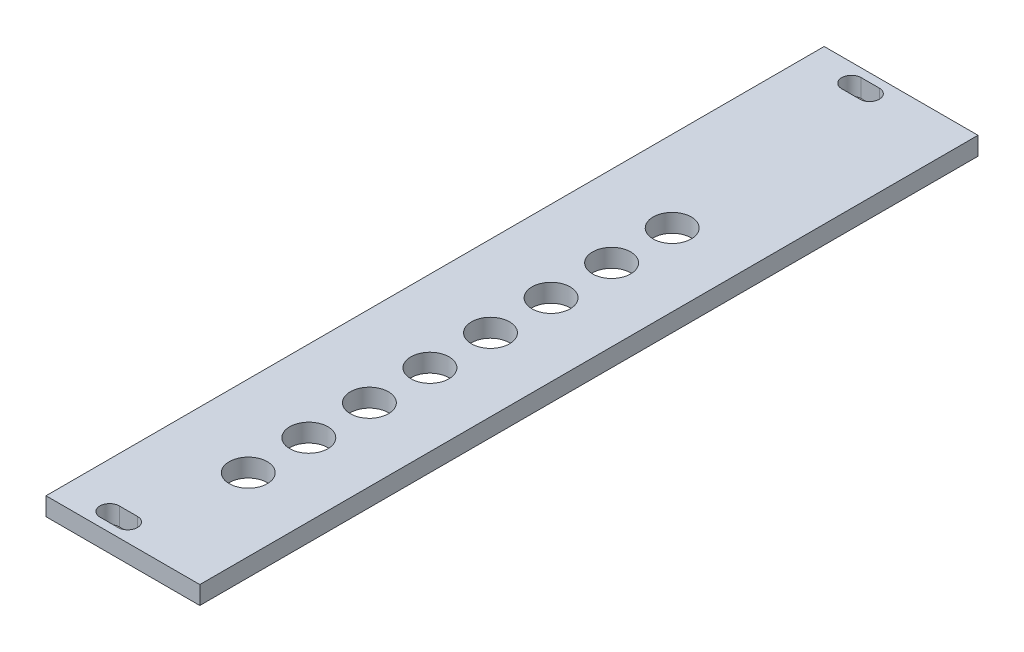
SolidWorks part; units mm, degrees
material "S235JR"
ref_plane "Vorderansicht (XY)" through (0, 0, 0) normal (0, 0, 1) x (1, 0, 0)
ref_plane "Draufansicht (XZ)" through (0, 0, 0) normal (0, 1, 0) x (1, 0, 0)
ref_plane "Seitenansicht (ZY)" through (0, 0, 0) normal (1, 0, 0) x (0, 0, -1)
sketch "Skizze1" plane through (0, 0, 0) normal (0, 1, 0) x (1, 0, 0)
  line L1 (-12.7, -64.25) -> (12.7, -64.25)
  line L2 (-12.7, -64.25) -> (-12.7, 64.25)
  line L3 (-12.7, 64.25) -> (12.7, 64.25)
  line L4 (12.7, -64.25) -> (12.7, 64.25)
  line L5 (-12.7, -64.25) -> (12.7, 64.25) construction
  line L6 (-12.7, 64.25) -> (12.7, -64.25) construction
  point P0 (0, 0)
  dimension "D1" = 128.5
  dimension "D2" = 25.4
extrude "Aufsatz-Linear austragen1" add sketch "Skizze1" along normal blind 3
sketch "Skizze2" plane through (0, 0, 0) normal (0, 1, 0) x (1, 0, 0)
  line L0 (-5.2, 61.25) -> (-2.2, 61.25) construction
  line L1 (-5.2, 62.85) -> (-2.2, 62.85)
  line L2 (-5.2, 59.65) -> (-2.2, 59.65)
  line L3 (-12.7, -64.25) -> (-12.7, 64.25) construction
  line L5 (-5.2, -61.25) -> (-2.2, -61.25) construction
  line L6 (-5.2, -59.65) -> (-2.2, -59.65)
  line L7 (-5.2, -62.85) -> (-2.2, -62.85)
  line L9 (12.7, 64.25) -> (-12.7, 64.25) construction
  line L10 (-12.7, -64.25) -> (12.7, -64.25) construction
  arc A0 (-5.2, 62.85) -> (-5.2, 59.65) centre (-5.2, 61.25) ccw
  arc A1 (-2.2, 59.65) -> (-2.2, 62.85) centre (-2.2, 61.25) ccw
  arc A2 (-5.2, -59.65) -> (-5.2, -62.85) centre (-5.2, -61.25) ccw
  arc A3 (-2.2, -62.85) -> (-2.2, -59.65) centre (-2.2, -61.25) ccw
  point P2 (-3.7, 61.25)
  point P13 (-3.7, -61.25)
  dimension "D1" = 7.5
  dimension "D2" = 3.2
  dimension "D3" = 3
  dimension "D4" = 3
  dimension "D5" = 7.5
  dimension "D6" = 3
  dimension "D7" = 3.2
  dimension "D8" = 3
extrude "Schnitt-Linear austragen4" cut sketch "Skizze2" along normal through all
sketch "Skizze3" plane through (0, 0, 0) normal (0, 1, 0) x (1, 0, 0)
  line L0 (-12.7, -64.25) -> (12.7, -64.25) construction
  line L1 (12.7, -64.25) -> (12.7, 64.25) construction
  circle A0 centre (0.7, -44.25) radius 3.15
  circle A1 centre (0.7, -34.25) radius 3.15
  circle A2 centre (0.7, -24.25) radius 3.15
  circle A3 centre (0.7, -14.25) radius 3.15
  circle A4 centre (0.7, -4.25) radius 3.15
  circle A5 centre (0.7, 5.75) radius 3.15
  circle A6 centre (0.7, 15.75) radius 3.15
  circle A7 centre (0.7, 25.75) radius 3.15
  dimension "D1" = 6.3
  dimension "D3" = 20
  dimension "D4" = 12
  dimension "D2" = 8
extrude "Schnitt-Linear austragen6" cut sketch "Skizze3" along normal through all
sketch "Skizze5" plane through (0, 0, 0) normal (0, 1, 0) x (1, 0, 0)
  line L0 (-7.6982, 50.7231) -> (-8.9305, 50.7231)
  line L1 (-10.1805, 51.9731) -> (-10.1805, 52.4731)
  line L2 (-8.9305, 53.7231) -> (-7.6982, 53.7231)
  line L3 (-6.8144, 54.0892) -> (-4.1805, 56.7231)
  line L4 (-4.1805, 56.7231) -> (-4.1805, 54.2408)
  line L5 (-4.5466, 53.357) -> (-6.8144, 51.0892)
  arc A0 (-4.1805, 54.2408) -> (-4.5466, 53.357) centre (-5.4305, 54.2408) cw
  arc A1 (-7.6982, 50.7231) -> (-6.8144, 51.0892) centre (-7.6982, 51.9731) ccw
  arc A2 (-7.6982, 53.7231) -> (-6.8144, 54.0892) centre (-7.6982, 54.9731) ccw
  arc A3 (-10.1805, 52.4731) -> (-8.9305, 53.7231) centre (-8.9305, 52.4731) cw
  arc A4 (-8.9305, 50.7231) -> (-10.1805, 51.9731) centre (-8.9305, 51.9731) cw
  text T0 "CTAG" font "Earthbound" height 3.5
  text T1 "Splitter\r\n" font "Earthbound" height 3.5
  text T2 "="
  text T3 "="
  text T4 "+"
  text T5 "="
  text T6 "+"
  text T7 "="
  text T8 "="
  text T9 "="
  point P18 (-4.1805, 53.7231)
  point P21 (-7.1805, 50.7231)
  point P24 (-7.1805, 53.7231)
  point P27 (-10.1805, 53.7231)
  point P30 (-10.1805, 50.7231)
  dimension "D7" = 1.25
  dimension "D1" = 3
  dimension "D2" = 3
  dimension "D3" = 3
  dimension "D4" = 3
  dimension "D5" = 3
  dimension "D6" = 3
